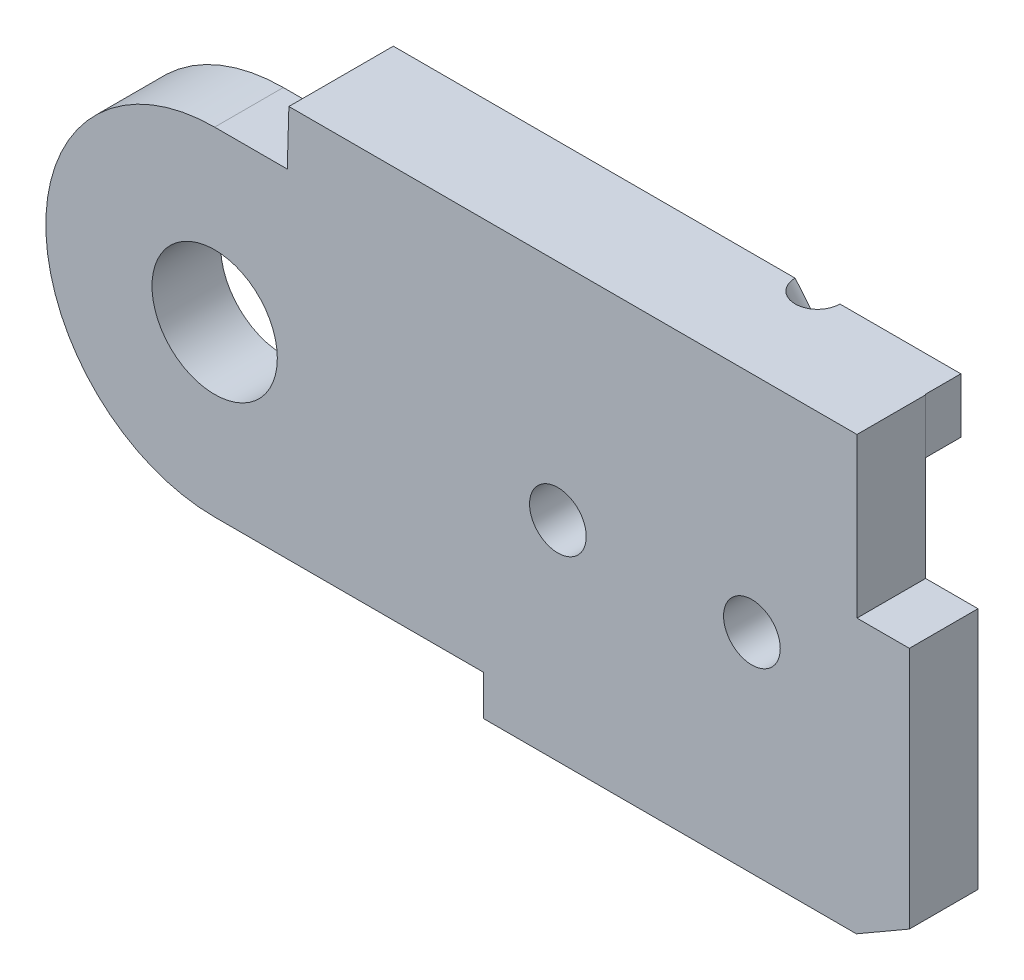
SolidWorks part; units mm, degrees
ref_plane "Front Plane" through (0, 0, 0) normal (0, 0, 1) x (1, 0, 0)
ref_plane "Top Plane" through (0, 0, 0) normal (0, 1, 0) x (1, 0, 0)
ref_plane "Right Plane" through (0, 0, 0) normal (1, 0, 0) x (0, 0, -1)
sketch "Sketch3" plane through (0, 0, 0) normal (0, 0, 1) x (1, 0, 0)
  line L7 (8, 0) -> (9, -2.5)
  line L11 (30, 7) -> (27, 7.5)
  line L13 (0, 7) -> (0, 7.5) construction
  line L14 (0, 7.5) -> (-22.3287, 7.5) construction
  line L15 (0, 5.3) -> (-14, 5.3) construction
  line L16 (0, 4) -> (-14, 4) construction
  line L17 (-14, 4) -> (-14, 5.3) construction
  line L18 (5.6569, 5.6569) -> (5.6569, 7.5)
  line L19 (5.6569, 7.5) -> (27, 7.5)
  line L20 (21.5, -7) -> (9, -7)
  line L21 (9, -7) -> (9, -2.5)
  line L23 (25.0503, -4.9497) -> (21.5, -7)
  arc A4 (8, 0) -> (5.6569, 5.6569) centre (0, 0) ccw
  arc A5 (25.0503, -4.9497) -> (30, 7) centre (30, 0) ccw
  circle A6 centre (0, 0) radius 7 construction
  circle A7 centre (0, 0) radius 3.9 construction
  circle A8 centre (0, 0) radius 5.3 construction
  circle A9 centre (0, 0) radius 4 construction
  dimension "D10" = 0.5
  dimension "D17" = 14
  dimension "D5" = 135
  dimension "D6" = 12.5
  dimension "D7" = 4.5
  dimension "D8" = 1
  dimension "D9" = 45
  dimension "D11" = 1.8431
  dimension "D12" = 30
  dimension "D14" = 3
extrude "Boss-Extrude1" add sketch "Sketch3" along normal blind 2 contours A5 L11 L19 L18 A4 L7 L21 L20 L23
sketch "Sketch20" plane through (0, 0, 0) normal (0, 0, 1) x (1, 0, 0)
  line L0 (0, 7) -> (0, 7.5) construction
  line L1 (0, 7.5) -> (-19.4737, 7.5) construction
  line L2 (0, 5.3) -> (-14, 5.3) construction
  line L3 (0, 4) -> (-14, 4) construction
  line L4 (-14, 4) -> (-14, 5.3) construction
  line L5 (0, 5.3) -> (17.4849, 5.3) construction
  line L6 (17.4849, 5.3) -> (17.4849, 4) construction
  line L7 (17.4849, 4) -> (0, 4) construction
  line L8 (-2.5, 7.5) -> (-2.5, 2.868) construction
  circle A0 centre (0, 0) radius 7 construction
  circle A1 centre (0, 0) radius 3.9 construction
  circle A3 centre (0, 0) radius 5.3 construction
  circle A4 centre (0, 0) radius 4 construction
  circle A5 centre (0, 0) radius 2 construction
  dimension "D1" = 0
  dimension "D2" = 2.5
ref_plane "Plane1" through (0, 0, 2) normal (0, 0, 1) x (1, 0, 0)
sketch "Sketch4" plane through (0, 0, 2) normal (0, 0, 1) x (1, 0, 0)
  line L4 (5.6569, 5.6569) -> (5.6569, 7.5)
  line L5 (5.6569, 5.6569) -> (5.6569, 7.5) construction
  line L6 (5.6569, 7.5) -> (21.5, 7.5)
  line L10 (8, 0) -> (9, -2.5)
  line L11 (9, -2.5) -> (9, -7)
  line L12 (9, -7) -> (21.5, -7)
  line L13 (21.5, -7) -> (21.5, 7.5)
  arc A0 (8, 0) -> (5.6569, 5.6569) centre (0, 0) ccw construction
  arc A3 (8, 0) -> (5.6569, 5.6569) centre (0, 0) ccw
sketch "Sketch22" plane through (0, 0, 2) normal (0, 0, 1) x (1, 0, 0)
  line L0 (5.6569, 5.6569) -> (2.4868, 5.6569)
  line L1 (5.6569, 7.5) -> (21.5, 7.5)
  line L2 (5.6569, 7.5) -> (2.4868, 7.5)
  line L3 (2.4868, 7.5) -> (2.4868, 5.6569)
  line L6 (8, 0) -> (9, -2.5)
  line L7 (9, -2.5) -> (9, -7)
  line L8 (9, -7) -> (21.5, -7)
  line L10 (21.5, 7.5) -> (27, 7.5)
  line L11 (27, 7.5) -> (27, 2.172)
  line L12 (27, 2.172) -> (23.2751, 2.172)
  line L13 (21.5, -7) -> (23.2751, -5.9749)
  line L14 (25.0503, -4.9497) -> (21.5, -7) construction
  line L15 (23.2751, -5.9749) -> (23.2751, 2.172)
  arc A0 (8, 0) -> (5.6569, 5.6569) centre (0, 0) ccw
extrude "Boss-Extrude6" add sketch "Sketch22" along normal blind 2.5
sketch "Sketch25" plane through (0, 0, 2) normal (0, 0, 1) x (1, 0, 0)
  line L0 (0, 5.3) -> (18.0981, 5.3) construction
  line L1 (0, 4) -> (18.0981, 4) construction
  line L2 (18.0981, 4) -> (18.0981, 5.3) construction
sketch "Sketch26" plane through (0, 0, 2) normal (0, 0, 1) x (1, 0, 0)
  line L1 (18.0981, 5.3) -> (2.5301, 5.3)
  line L2 (18.0981, 4) -> (2.5301, 4)
  line L3 (2.5301, 5.3) -> (2.5301, 4)
  line L4 (18.0981, 5.3) -> (27, 5.3)
  line L5 (27, 2.172) -> (27, 7.5) construction
  line L6 (27, 5.3) -> (27, 4)
  line L7 (27, 4) -> (18.0981, 4)
extrude "Cut-Extrude6" cut sketch "Sketch26" along normal blind 2.5
ref_plane "Plane18" through (0, 0, 4.5) normal (0, 0, 1) x (1, 0, 0)
sketch "Sketch31" plane through (0, 0, 4.5) normal (0, 0, 1) x (1, 0, 0)
  line L0 (2.4327, 5.6569) -> (0, 5.6569)
  line L4 (9, -5.6569) -> (0, -5.6569)
  line L5 (2.4327, 5.6569) -> (2.4868, 7.5)
  line L12 (9, -7) -> (9, -5.6569)
  line L13 (9, -2.5) -> (9, -7) construction
  line L16 (27, 7.5) -> (27, 2.172)
  line L17 (27, 2.172) -> (23.2751, 2.172)
  line L18 (23.2751, -5.9749) -> (23.2751, 2.172)
  line L19 (27, 7.5) -> (2.4868, 7.5)
  line L20 (9, -7) -> (21.5, -7)
  line L21 (21.5, -7) -> (23.2751, -5.9749)
  arc A0 (0, 5.6569) -> (0, -5.6569) centre (0, 0) ccw
  dimension "D1" = 5.6569
extrude "Boss-Extrude14" add sketch "Sketch31" along normal blind 2.3 separate body
sketch "Sketch32" plane through (0, 0, 6.8) normal (0, 0, 1) x (1, 0, 0)
  circle A0 centre (0, 0) radius 2.1
extrude "Cut-Extrude7" cut sketch "Sketch32" against normal blind 2.3
sketch "Sketch33" plane through (0, 0, 6.8) normal (0, 0, 1) x (1, 0, 0)
  line L4 (9, -5.6569) -> (9, -7)
  line L11 (9, -7) -> (21.5, -7)
  line L15 (21.5, -7) -> (21.5, -5.6569)
  line L16 (21.5, -5.6569) -> (9, -5.6569)
  line L17 (2.4868, 7.5) -> (21.5, 7.5)
  line L18 (27, 7.5) -> (2.4868, 7.5) construction
  line L19 (2.4868, 7.5) -> (2.4327, 5.6569)
  line L20 (2.4327, 5.6569) -> (21.5, 5.6569)
  line L21 (21.5, 5.6569) -> (21.5, 7.5)
extrude "Boss-Extrude15" add sketch "Sketch33" along normal blind 1.2
sketch "Sketch34" plane through (0, 0, 2) normal (0, 0, 1) x (1, 0, 0)
  line L0 (30, 5.3) -> (18.0981, 5.3) construction
  line L1 (30, 4) -> (18.0981, 4) construction
  circle A0 centre (30, 0) radius 2 construction
  circle A1 centre (30, 0) radius 5.3 construction
  circle A2 centre (30, 0) radius 4 construction
sketch "Sketch35" plane through (0, 0, 6.8) normal (0, 0, 1) x (1, 0, 0)
  line L0 (27, 2.172) -> (27, 7.5)
  line L1 (27, 2.172) -> (21.5204, 2.172)
  line L2 (27, 7.5) -> (21.5204, 7.5)
  line L3 (21.5204, 2.172) -> (21.5204, 7.5)
  line L4 (27, 2.172) -> (27, 7.5) construction
  line L5 (27, 7.5) -> (21.5, 7.5) construction
  dimension "D1" = 0
extrude "Cut-Extrude8" cut sketch "Sketch35" against normal blind 2.4
sketch "Sketch36" plane through (0, 0, 4.4) normal (0, 0, 1) x (1, 0, 0)
  line L0 (27, 2.172) -> (27, 4)
  line L1 (27, 2.172) -> (23.3, 2.172)
  line L2 (27, 4) -> (23.3, 4)
  line L3 (23.3, 2.172) -> (23.3, 4)
  line L4 (21.5, -7) -> (21.5, 7.5) construction
  dimension "D1" = 1.8
extrude "Cut-Extrude9" cut sketch "Sketch36" against normal blind 2.4
sketch "Sketch37" plane through (0, 0, 2) normal (0, 0, 1) x (1, 0, 0)
  circle A0 centre (30, 0) radius 3.9
extrude "Boss-Extrude16" add sketch "Sketch37" along normal blind 2.3
sketch "Sketch39" plane through (0, 0, 4.3) normal (0, 0, 1) x (1, 0, 0)
  line L0 (29, 1.7321) -> (29, -1.7321)
  arc A0 (29, -1.7321) -> (29, 1.7321) centre (30, 0) ccw
  dimension "D2" = 4
  dimension "D1" = 1
extrude "Cut-Extrude10" cut sketch "Sketch39" against normal through all
sketch "Sketch43" plane through (0, 0, 6.8) normal (0, 0, 1) x (1, 0, 0)
  line L2 (0, -5.6569) -> (9, -5.6569) construction
  circle A0 centre (11.5, 0) radius 2.5
  circle A1 centre (18, 0) radius 2.5
  dimension "D1" = 2.5
  dimension "D3" = 5
  dimension "D4" = 6.5
  dimension "D2" = 5.6569
extrude "Boss-Extrude17" add sketch "Sketch43" along normal blind 1.2
sketch "Sketch44" plane through (0, 0, 8) normal (0, 0, 1) x (1, 0, 0)
  circle A0 centre (11.5, 0) radius 0.95
  circle A1 centre (18, 0) radius 0.95
  dimension "D1" = 1.9
  dimension "D2" = 1.9
extrude "Cut-Extrude11" cut sketch "Sketch44" against normal through all
sketch "Sketch45" plane through (0, 0, 0) normal (0, 0, -1) x (-1, 0, 0)
  circle A0 centre (-11.5, 0) radius 2
  circle A1 centre (-18, 0) radius 2
extrude "Cut-Extrude12" cut sketch "Sketch45" against normal blind 2.5
ref_plane "Plane17" through (0, 0, 8) normal (0, 0, 1) x (1, 0, 0)
sketch "Sketch48" plane through (0, 0, 2) normal (0, 0, 1) x (1, 0, 0)
  circle A0 centre (30, 0) radius 5 construction
sketch "Sketch51" plane through (0, 0, 8) normal (0, 0, 1) x (1, 0, 0)
  line L0 (18.2355, 5.6569) -> (27.0112, -4.8677) construction
  line L1 (2.4327, 5.6569) -> (21.5, 5.6569) construction
sketch "Sketch52" plane through (0, 5.6569, 0) normal (0, -1, 0) x (1, 0, 0)
  circle A0 centre (18.2355, 8) radius 0.75
extrude "Cut-Extrude13" cut sketch "Sketch52" along direction (0.6404, -0.768, 0) on the side against the normal blind 10
split "Split1" trim tools "Plane18" bodies to split 133 129 resulting bodies 135 136
mirror "Mirror1" about plane through (0, 0, 8) normal (0, 0, 1) of bodies 135 136
delete or keep bodies "Body-Delete/Keep 1" type delete bodies bodies 135 136 138
